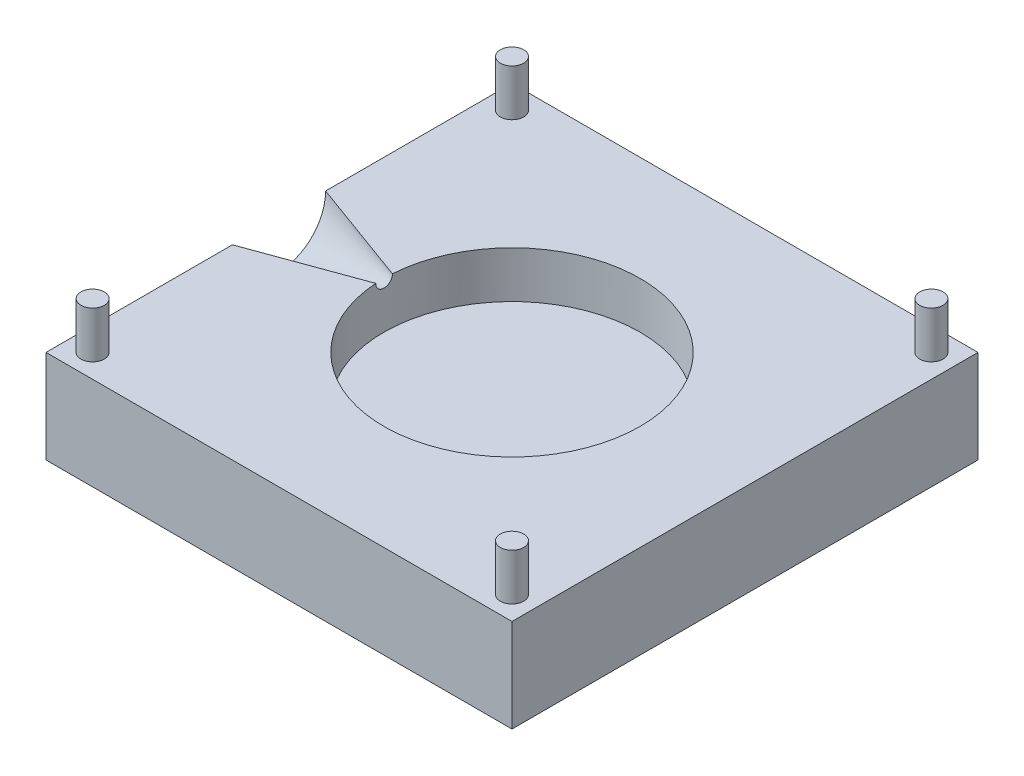
SolidWorks part; units mm, degrees
ref_plane "Front Plane" through (0, 0, 0) normal (0, 0, 1) x (1, 0, 0)
ref_plane "Top Plane" through (0, 0, 0) normal (0, 1, 0) x (1, 0, 0)
ref_plane "Right Plane" through (0, 0, 0) normal (1, 0, 0) x (0, 0, -1)
sketch "Sketch1" plane through (0, 0, 0) normal (0, 1, 0) x (1, 0, 0)
  line L1 (-40, -40) -> (40, -40)
  line L2 (-40, -40) -> (-40, 40)
  line L3 (-40, 40) -> (40, 40)
  line L4 (40, -40) -> (40, 40)
  line L5 (-40, -40) -> (40, 40) construction
  line L6 (-40, 40) -> (40, -40) construction
  point P0 (0, 0)
  dimension "D1" = 80
extrude "Boss-Extrude1" add sketch "Sketch1" along normal blind 15 draft 5 draft outward yes
sketch "Sketch2" plane through (0, 15, 0) normal (0, 1, 0) x (1, 0, 0)
  line L1 (-6.75, -36) -> (6.75, -36)
  line L2 (-6.75, -36) -> (-6.75, 36)
  line L3 (-6.75, 36) -> (6.75, 36)
  line L4 (6.75, -36) -> (6.75, 36)
  line L5 (-6.75, -36) -> (6.75, 36) construction
  line L6 (-6.75, 36) -> (6.75, -36) construction
  line L7 (-36, -6.75) -> (36, -6.75)
  line L8 (-36, -6.75) -> (-36, 6.75)
  line L9 (-36, 6.75) -> (36, 6.75)
  line L10 (36, -6.75) -> (36, 6.75)
  line L11 (-36, -6.75) -> (36, 6.75) construction
  line L12 (-36, 6.75) -> (36, -6.75) construction
  point P0 (0, 0)
  point P6 (0, 0)
  dimension "D1" = 72
  dimension "D2" = 72
  dimension "D3" = 13.5
  dimension "D4" = 13.5
extrude "Cut-Extrude1" cut sketch "Sketch2" against normal blind 10 draft 5 contours L9 L8 L7 L2 | L2 L9 L4 L3 | L9 L2 L7 L4 | L7 L10 L9 L4 | L7 L2 L1 L4
sketch "Sketch3" plane through (0, 0, 0) normal (0, -1, 0) x (1, 0, 0)
  circle A0 centre (0, 0) radius 27.5
  dimension "D1" = 55
extrude "Boss-Extrude2" add sketch "Sketch3" along normal blind 10
sketch "Sketch4" plane through (0, 0, 0) normal (0, -1, 0) x (1, 0, 0)
  line L1 (-50, -50) -> (50, -50)
  line L2 (-50, -50) -> (-50, 50)
  line L3 (-50, 50) -> (50, 50)
  line L4 (50, -50) -> (50, 50)
  line L5 (-50, -50) -> (50, 50) construction
  line L6 (-50, 50) -> (50, -50) construction
  point P0 (0, 0)
  dimension "D1" = 100
extrude "Boss-Extrude3" add sketch "Sketch4" along normal blind 20 separate body
combine bodies "Combine1" operation type subtract main body 104 bodies to subtract 103
sketch "Sketch5" plane through (0, 0, 0) normal (0, 1, 0) x (1, 0, 0)
  line L0 (-50, 50) -> (50, 50) construction
  line L1 (-50, -50) -> (-50, 50) construction
  circle A0 centre (-45, 45) radius 2.5
  dimension "D1" = 5
  dimension "D2" = 5
  dimension "D3" = 5
extrude "Boss-Extrude4" add sketch "Sketch5" along normal blind 10
pattern_circular "CirPattern1" count 4 over 360 about axis through (0, 0, 0) along (0, 1, 0) of "Boss-Extrude4"
sketch "Sketch6" plane through (-50, 0, 0) normal (-1, 0, 0) x (0, 0, 1)
  line L0 (50, 0) -> (-50, 0) construction
  circle A0 centre (0, 0) radius 10
extrude "Cut-Extrude2" cut sketch "Sketch6" against normal blind 25 draft 20
